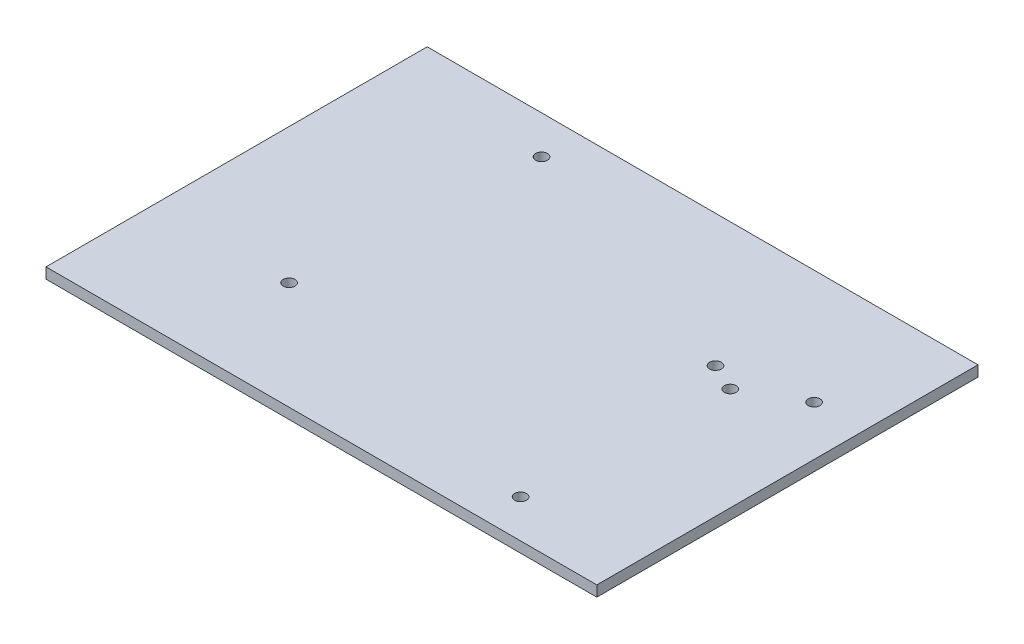
SolidWorks part; units mm, degrees
ref_plane "Front" through (0, 0, 0) normal (0, 0, 1) x (1, 0, 0)
ref_plane "Top" through (0, 0, 0) normal (0, 1, 0) x (1, 0, 0)
ref_plane "Right" through (0, 0, 0) normal (1, 0, 0) x (0, 0, -1)
sketch "Sketch1" plane through (0, 0, 0) normal (0, 1, 0) x (1, 0, 0)
  line L1 (-72.25, -50) -> (72.25, -50)
  line L2 (-72.25, -50) -> (-72.25, 50)
  line L3 (-72.25, 50) -> (72.25, 50)
  line L4 (72.25, -50) -> (72.25, 50)
  line L5 (-72.25, -50) -> (72.25, 50) construction
  line L6 (-72.25, 50) -> (72.25, -50) construction
  circle A0 centre (-32.25, 40) radius 1.55
  circle A1 centre (59.25, 20) radius 1.55
  circle A2 centre (42.25, -40) radius 1.55
  point P0 (0, 0)
  dimension "D3" = 3.1
  dimension "D4" = 3.1
  dimension "D5" = 3.1
  dimension "D6" = 10
  dimension "D7" = 40
  dimension "D8" = 13
  dimension "D9" = 30
  dimension "D10" = 10
  dimension "D11" = 30
  dimension "D1" = 100
  dimension "D2" = 144.5
extrude "Boss-Extrude1" add sketch "Sketch1" along normal blind 2.8
sketch "Sketch2" plane through (0, 2.8, 0) normal (0, 1, 0) x (1, 0, 0)
  line L0 (-72.25, -50) -> (72.25, -50) construction
  line L1 (-72.25, 50) -> (-72.25, -50) construction
  circle A0 centre (-36.75, -21.73) radius 1.55
  dimension "D1" = 3.1
  dimension "D3" = 35.5
  dimension "D2" = 28.27
extrude "Cut-Extrude1" cut sketch "Sketch2" against normal up to next
sketch "Sketch3" plane through (0, 2.8, 0) normal (0, 1, 0) x (1, 0, 0)
  line L0 (72.25, -50) -> (72.25, 50) construction
  line L1 (45.25, 12) -> (37.9995, 15.3809) construction
  line L2 (72.25, 50) -> (-72.25, 50) construction
  circle A0 centre (37.9995, 15.3809) radius 1.55
  circle A1 centre (45.25, 12) radius 1.55
  dimension "D1" = 3.1
  dimension "D2" = 3.1
  dimension "D3" = 27
  dimension "D4" = 8
  dimension "D5" = 65
  dimension "D6" = 38
extrude "Cut-Extrude2" cut sketch "Sketch3" against normal up to next
